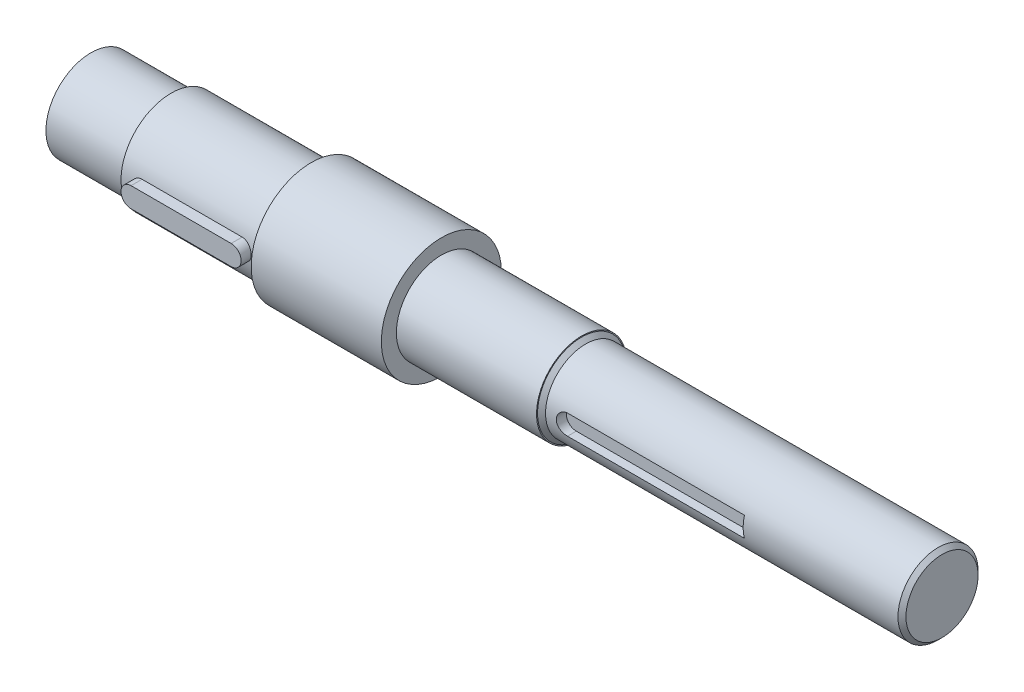
SolidWorks part; units mm, degrees
ref_plane "Front Plane" through (0, 0, 0) normal (0, 0, 1) x (1, 0, 0)
ref_plane "Top Plane" through (0, 0, 0) normal (0, 1, 0) x (1, 0, 0)
ref_plane "Right Plane" through (0, 0, 0) normal (1, 0, 0) x (0, 0, -1)
sketch "Sketch2" plane through (0, 0, 0) normal (0, 1, 0) x (1, 0, 0)
  line L0 (0, 0) -> (0, 22.5)
  line L1 (0, 22.5) -> (40, 22.5)
  line L2 (40, 22.5) -> (40, 25)
  line L3 (40, 25) -> (110, 25)
  line L4 (110, 25) -> (110, 30)
  line L5 (110, 30) -> (175, 30)
  line L6 (175, 30) -> (175, 22.5)
  line L7 (175, 22.5) -> (245, 22.5)
  line L8 (245, 22.5) -> (245, 20)
  line L9 (245, 20) -> (325, 20)
  line L11 (325, 0) -> (0, 0)
  line L12 (325, 20) -> (425, 20)
  line L13 (425, 20) -> (425, 0)
  line L14 (425, 0) -> (325, 0)
  line L15 (303.786, 20) -> (303.786, 0)
  dimension "D1" = 40
  dimension "D2" = 70
  dimension "D3" = 65
  dimension "D4" = 70
  dimension "D5" = 80
  dimension "D6" = 25
  dimension "D7" = 22.5
  dimension "D8" = 30
  dimension "D9" = 20
  dimension "D10" = 22.5
  dimension "D11" = 100
revolve "Revolve1" add sketch "Sketch2" angle 360 about L11
chamfer "Chamfer1" distance 2 angle 45 2 edges at (425, 0, -20) (245, 0, -20)
ref_plane "Plane1" through (0, 0, 25) normal (0, 0, 1) x (1, 0, 0)
ref_plane "Plane3" through (0, 0, 20) normal (0, 0, 1) x (1, 0, 0)
sketch "Sketch4" plane through (0, 0, 20) normal (0, 0, 1) x (1, 0, 0)
  line L0 (282.2967, 0) -> (333.6992, 0) construction
  line L2 (257.357, -5) -> (345.6932, -5)
  line L4 (257.357, 5) -> (345.6932, 5)
  line L5 (345.6932, -5) -> (345.6932, 5)
  line L6 (257.357, -5) -> (345.6932, 5) construction
  line L7 (257.357, 5) -> (345.6932, -5) construction
  arc A0 (257.357, 5) -> (257.357, -5) centre (257.357, 0) ccw
  point P1 (301.5251, 0)
  dimension "D1" = 10
extrude "Cut-Extrude2" cut sketch "Sketch4" against normal blind 5
sketch "Sketch5" plane through (0, 0, 25) normal (0, 0, 1) x (1, 0, 0)
  line L0 (0, 0) -> (-119.2608, 0) construction
  line L1 (110, 30) -> (110, -30) construction
  line L2 (50, 5) -> (100, 5)
  line L4 (50, -5) -> (100, -5)
  line L6 (50, 5) -> (100, -5) construction
  line L7 (50, -5) -> (100, 5) construction
  arc A0 (100, -5) -> (100, 5) centre (100, 0) ccw
  arc A1 (50, 5) -> (50, -5) centre (50, 0) ccw
  point P1 (75, 0)
  dimension "D3" = 10
  dimension "D4" = 10
  dimension "D1" = 50
  dimension "D2" = 10
  dimension "D5" = 10
extrude "Cut-Extrude3" cut sketch "Sketch5" against normal blind 5
ref_plane "Plane4" through (50, 5, 20) normal (-1, 0, 0) x (0, 0, 1)
sketch "Sketch8" plane through (0, 0, 20) normal (0, 0, 1) x (1, 0, 0)
  line L2 (100, 5) -> (50, 5)
  line L3 (50, -5) -> (100, -5)
  line L4 (100, 5) -> (50, 5)
  line L5 (50, -5) -> (100, -5)
  arc A2 (100, -5) -> (100, 5) centre (100, 0) ccw
  arc A3 (50, 5) -> (50, -5) centre (50, 0) ccw
  arc A4 (100, -5) -> (100, 5) centre (100, 0) ccw
  arc A5 (50, 5) -> (50, -5) centre (50, 0) ccw
  dimension "D1" = 0
extrude "Boss-Extrude1" add sketch "Sketch8" along normal blind 10
